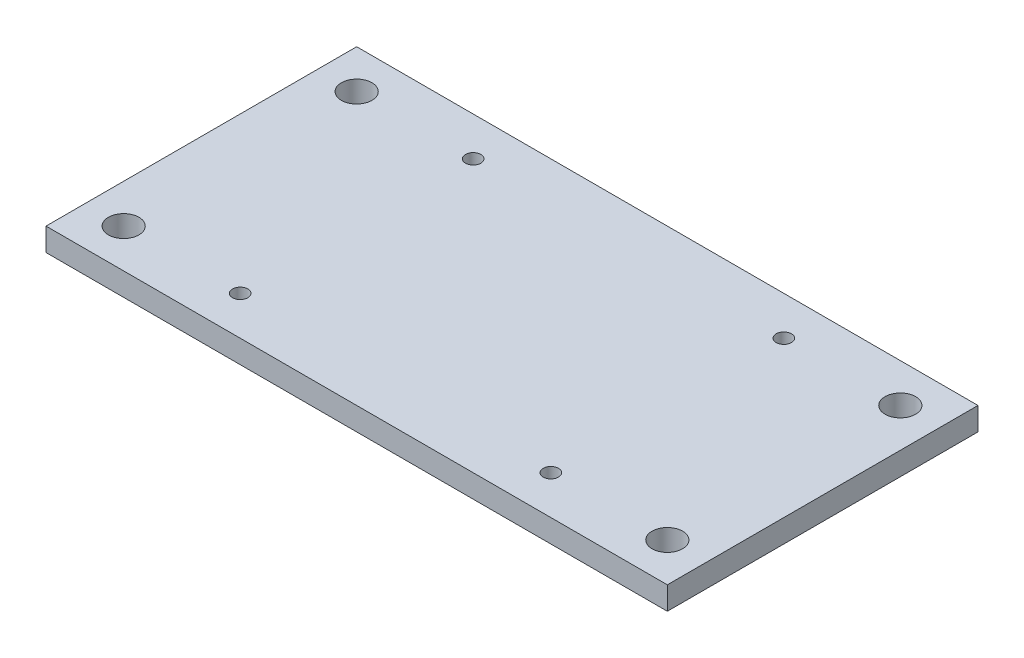
SolidWorks part; units mm, degrees
ref_plane "Front Plane" through (0, 0, 0) normal (0, 0, 1) x (1, 0, 0)
ref_plane "Top Plane" through (0, 0, 0) normal (0, 1, 0) x (1, 0, 0)
ref_plane "Right Plane" through (0, 0, 0) normal (1, 0, 0) x (0, 0, -1)
sketch "Sketch1" plane through (0, 0, 0) normal (0, 1, 0) x (1, 0, 0)
  line L0 (0, 10.16) -> (40.64, 10.16) construction
  line L1 (0, 0) -> (40.64, 0)
  line L2 (0, 0) -> (0, 20.32)
  line L3 (0, 20.32) -> (40.64, 20.32)
  line L4 (40.64, 0) -> (40.64, 20.32)
  line L5 (20.32, 0) -> (20.32, 20.32) construction
  line L6 (2.54, 2.54) -> (13.2165, 2.54) construction
  line L7 (38.1, 17.78) -> (38.1, 2.54) construction
  circle A0 centre (2.54, 2.54) radius 1
  circle A1 centre (38.1, 2.54) radius 1
  circle A2 centre (38.1, 17.78) radius 1
  circle A3 centre (2.54, 17.78) radius 1
  circle A4 centre (10.16, 2.54) radius 0.5
  circle A5 centre (10.16, 17.78) radius 0.5
  circle A6 centre (30.48, 2.54) radius 0.5
  circle A7 centre (30.48, 17.78) radius 0.5
  dimension "D3" = 2
  dimension "D6" = 1
  dimension "D1" = 40.64
  dimension "D2" = 20.32
  dimension "D4" = 2.54
  dimension "D5" = 2.54
  dimension "D7" = 7.62
extrude "Boss-Extrude1" add sketch "Sketch1" along normal blind 1.5
